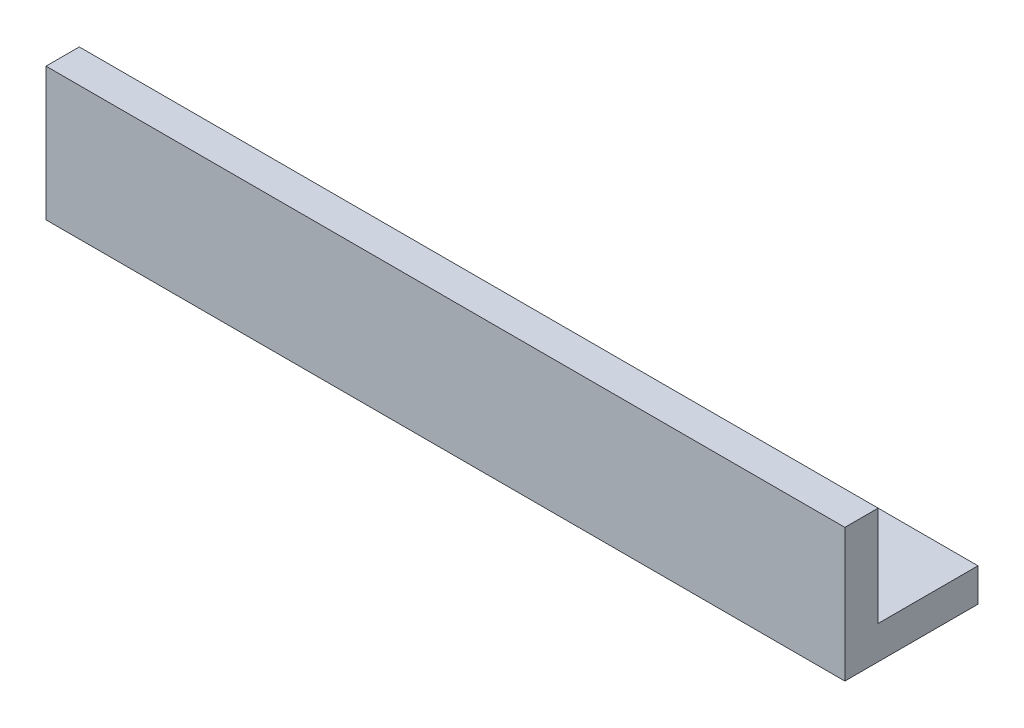
SolidWorks part; units mm, degrees
ref_plane "Front Plane" through (0, 0, 0) normal (0, 0, 1) x (1, 0, 0)
ref_plane "Top Plane" through (0, 0, 0) normal (0, 1, 0) x (1, 0, 0)
ref_plane "Right Plane" through (0, 0, 0) normal (1, 0, 0) x (0, 0, -1)
sketch "Sketch1" plane through (0, 0, 0) normal (0, 0, 1) x (1, 0, 0)
  line L1 (-4.4135, 28.7043) -> (71.7865, 28.7043)
  line L2 (-4.4135, 28.7043) -> (-4.4135, 16.0043)
  line L3 (-4.4135, 16.0043) -> (71.7865, 16.0043)
  line L4 (71.7865, 28.7043) -> (71.7865, 16.0043)
  dimension "D1" = 76.2
  dimension "D2" = 12.7
extrude "Boss-Extrude1" add sketch "Sketch1" along normal blind 3.175
ref_plane "Plane1" through (71.7865, 16.0043, 3.175) normal (1, 0, 0) x (0, 0, -1)
ref_plane "Plane2" through (-4.4135, 28.7043, 3.175) normal (0, 0, -1) x (-1, 0, 0)
ref_plane "Plane3" through (-4.4135, 16.0043, 3.175) normal (1, 0, 0) x (0, 0, -1)
sketch "Sketch7" plane through (0, 16.0043, 0) normal (0, -1, 0) x (-1, 0, 0)
  line L0 (4.4135, 0) -> (-71.7865, 0) construction
  line L1 (4.4135, 9.525) -> (-71.7865, 9.525)
  line L2 (4.4135, 9.525) -> (4.4135, 0)
  line L3 (4.4135, 0) -> (-71.7865, 0)
  line L4 (-71.7865, 9.525) -> (-71.7865, 0)
  dimension "D1" = 76.2
  dimension "D2" = 9.525
  dimension "D3" = 0
  dimension "D4" = 0
extrude "Boss-Extrude2" add sketch "Sketch7" against normal blind 3.175
